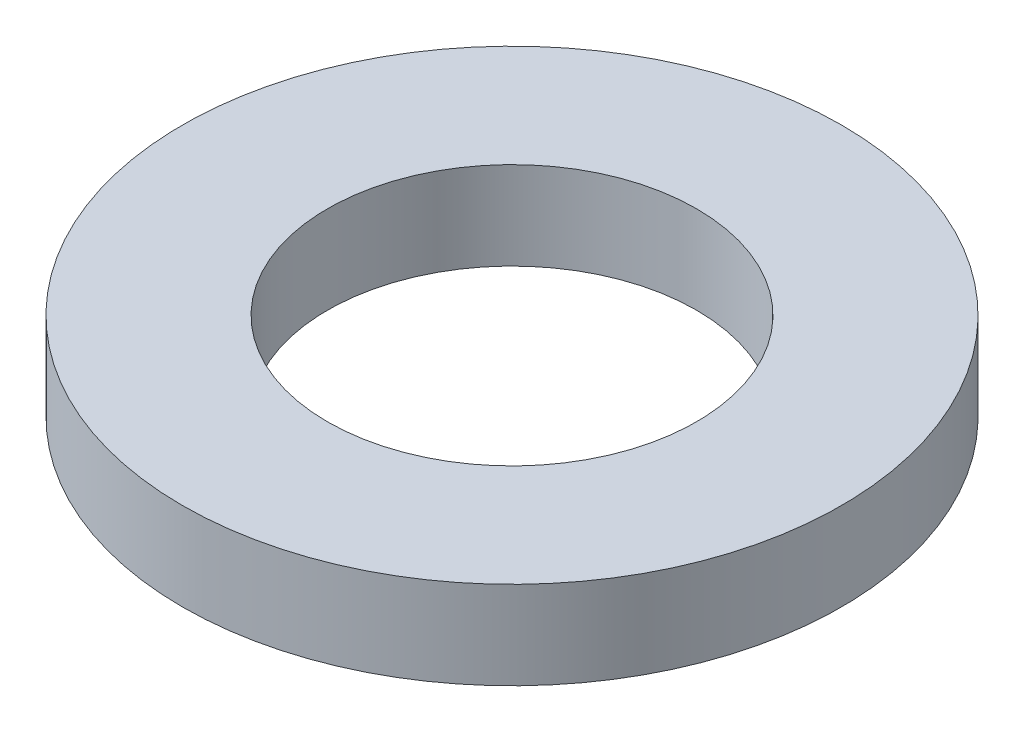
SolidWorks part; units mm, degrees
material " 40Х ГОСТ 4543-71"
ref_plane "Спереди" through (0, 0, 0) normal (0, 0, 1) x (1, 0, 0)
ref_plane "Сверху" through (0, 0, 0) normal (0, 1, 0) x (1, 0, 0)
ref_plane "Слева" through (0, 0, 0) normal (1, 0, 0) x (0, 0, -1)
sketch "Эскиз1" plane through (0, 0, 0) normal (0, 1, 0) x (1, 0, 0)
  circle A0 centre (0, 0) radius 7.5
  circle A1 centre (0, 0) radius 4.2
  dimension "D1" = 15
  dimension "D2" = 8.4
extrude "Вытянуть1" add sketch "Эскиз1" along normal blind 2
